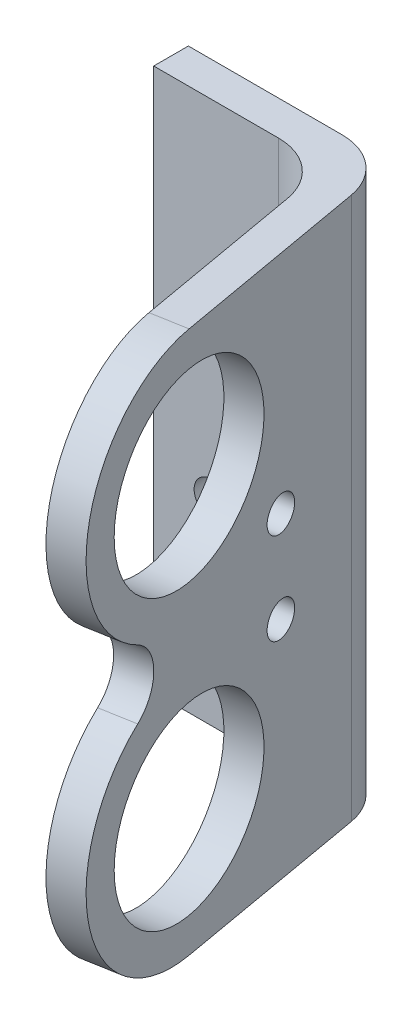
SolidWorks part; units mm, degrees
material "Acrylic (Medium-high impact)"
ref_plane "Front Plane" through (0, 0, 0) normal (0, 0, 1) x (1, 0, 0)
ref_plane "Top Plane" through (0, 0, 0) normal (0, 1, 0) x (1, 0, 0)
ref_plane "Right Plane" through (0, 0, 0) normal (1, 0, 0) x (0, 0, -1)
sketch "Sketch1" plane through (0, 0, 0) normal (0, 1, 0) x (1, 0, 0)
  line L0 (-2.3206, 10.9135) -> (11.0012, 10.9135)
  line L1 (15.9252, 6.7817) -> (20.8433, -21.1098)
  line L2 (20.8433, -21.1098) -> (17.8888, -21.6308)
  line L3 (17.8888, -21.6308) -> (13.4079, 3.7817)
  line L4 (8.4839, 7.9135) -> (-2.3206, 7.9135)
  line L5 (-2.3206, 7.9135) -> (-2.3206, 10.9135)
  arc A0 (15.9252, 6.7817) -> (11.0012, 10.9135) centre (11.0012, 5.9135) ccw
  arc A1 (13.4079, 3.7817) -> (8.4839, 7.9135) centre (8.4839, 2.9135) ccw
  dimension "D5" = 5
  dimension "D1" = 3
  dimension "D2" = 100
extrude "Boss-Extrude1" add sketch "Sketch1" along normal blind 47
sketch "Sketch2" plane through (0, 0, -7.9135) normal (0, 0, 1) x (1, 0, 0)
  line L0 (-2.3206, 47) -> (-2.3206, 0) construction
  line L1 (2.6794, 30) -> (2.6794, 47) construction
  line L2 (-2.3206, 47) -> (8.4839, 47) construction
  line L3 (2.6794, 17) -> (2.6794, 0) construction
  line L4 (-2.3206, 0) -> (8.4839, 0) construction
  circle A0 centre (2.6794, 30) radius 1.5
  circle A1 centre (2.6794, 17) radius 1.5
  dimension "D2" = 3
  dimension "D1" = 5
  dimension "D3" = 13
extrude "Cut-Extrude1" cut sketch "Sketch2" against normal through all
sketch "Sketch3" plane through (13.6504, 0, -2.4069) normal (-0.9848, 0, 0.1736) x (0.1736, 0, 0.9848)
  line L0 (13.4085, 11) -> (13.4085, 0) construction
  line L1 (-1.396, 0) -> (24.4085, 0) construction
  line L2 (13.4085, 36) -> (13.4085, 47) construction
  line L3 (-1.396, 47) -> (24.4085, 47) construction
  line L4 (24.4085, 47) -> (24.4085, 0) construction
  line L5 (13.4085, 47) -> (24.4085, 47)
  line L6 (24.4085, 47) -> (24.4085, 36)
  line L7 (13.4085, 0) -> (24.4085, 0)
  line L8 (24.4085, 0) -> (24.4085, 11)
  circle A0 centre (13.4085, 36) radius 8
  circle A1 centre (13.4085, 11) radius 8
  circle A2 centre (13.4085, 36) radius 11
  circle A3 centre (13.4085, 11) radius 11
  arc A4 (18.8949, 20.5342) -> (18.8949, 26.4658) centre (20.6015, 23.5) cw
  line M3 (-1.396, 0) -> (24.4085, 0)
  line M4 (24.4085, 0) -> (24.4085, 47)
  line M5 (24.4085, 47) -> (-1.396, 47)
  dimension "D1" = 16
  dimension "D2" = 22
  dimension "D3" = 25
extrude "Cut-Extrude2" cut sketch "Sketch3" against normal through all contours A2 M4 M5 | A3 M3 M4 | A1 | A0 | A4 A3 A2 M4
sketch "Sketch4" plane through (13.6504, 0, -2.4069) normal (-0.9848, 0, 0.1736) x (0.1736, 0, 0.9848)
  line L0 (-1.396, 47) -> (-1.396, 0) construction
  circle A0 centre (3.604, 27.4635) radius 1.47
  circle A2 centre (3.604, 19.5365) radius 1.47
  circle A3 centre (13.4085, 11) radius 8 construction
  circle A5 centre (13.4085, 36) radius 8 construction
  dimension "D1" = 5
  dimension "D2" = 5
  dimension "D3" = 13
  dimension "D4" = 13
  dimension "D5" = 2.94
extrude "Cut-Extrude3" cut sketch "Sketch4" against normal through all
